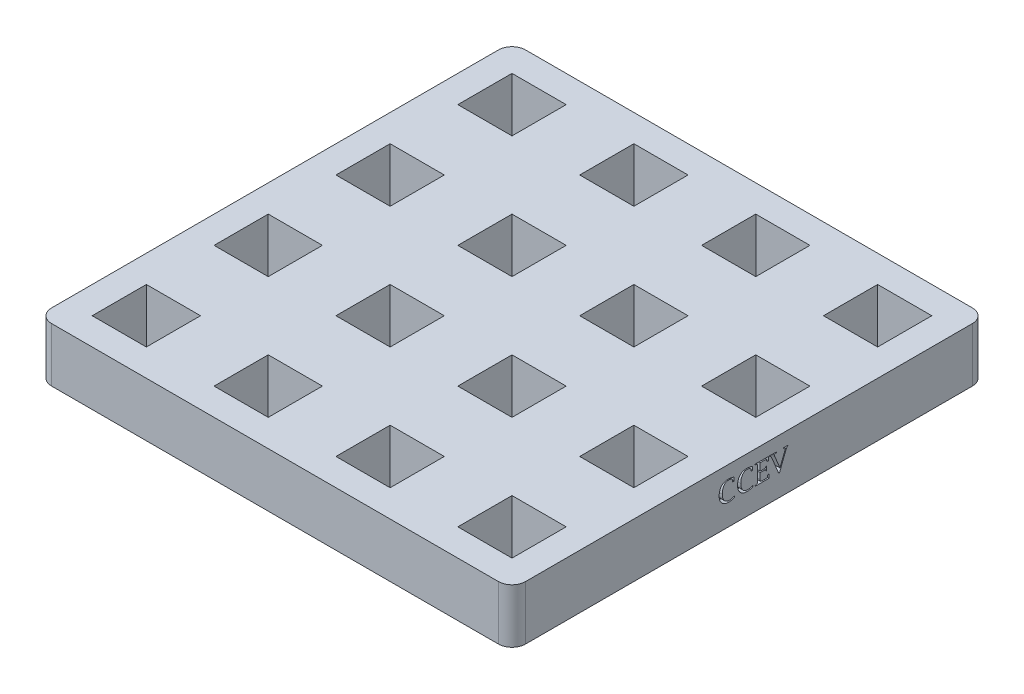
SolidWorks part; units mm, degrees
ref_plane "Front Plane" through (0, 0, 0) normal (0, 0, 1) x (1, 0, 0)
ref_plane "Top Plane" through (0, 0, 0) normal (0, 1, 0) x (1, 0, 0)
ref_plane "Right Plane" through (0, 0, 0) normal (1, 0, 0) x (0, 0, -1)
sketch "Sketch1" plane through (0, 0, 0) normal (0, 1, 0) x (1, 0, 0)
  line L0 (27.94, -5.08) -> (27.94, -15.24)
  line L1 (0, 0) -> (88.9, 0)
  line L2 (0, 0) -> (0, -88.9)
  line L3 (0, -88.9) -> (88.9, -88.9)
  line L4 (88.9, 0) -> (88.9, -88.9)
  line L5 (5.08, -5.08) -> (15.24, -5.08)
  line L6 (5.08, -5.08) -> (5.08, -15.24)
  line L7 (5.08, -15.24) -> (15.24, -15.24)
  line L8 (15.24, -5.08) -> (15.24, -15.24)
  line L9 (27.94, -5.08) -> (38.1, -5.08)
  line L10 (38.1, -5.08) -> (38.1, -15.24)
  line L11 (27.94, -15.24) -> (38.1, -15.24)
  line L12 (50.8, -5.08) -> (50.8, -15.24)
  line L13 (50.8, -5.08) -> (60.96, -5.08)
  line L14 (60.96, -5.08) -> (60.96, -15.24)
  line L15 (50.8, -15.24) -> (60.96, -15.24)
  line L16 (73.66, -5.08) -> (73.66, -15.24)
  line L17 (73.66, -5.08) -> (83.82, -5.08)
  line L18 (83.82, -5.08) -> (83.82, -15.24)
  line L19 (73.66, -15.24) -> (83.82, -15.24)
  line L20 (27.94, -27.94) -> (27.94, -38.1)
  line L21 (27.94, -27.94) -> (38.1, -27.94)
  line L22 (38.1, -27.94) -> (38.1, -38.1)
  line L23 (27.94, -38.1) -> (38.1, -38.1)
  line L24 (50.8, -27.94) -> (50.8, -38.1)
  line L25 (50.8, -27.94) -> (60.96, -27.94)
  line L26 (60.96, -27.94) -> (60.96, -38.1)
  line L27 (50.8, -38.1) -> (60.96, -38.1)
  line L28 (73.66, -27.94) -> (73.66, -38.1)
  line L29 (73.66, -27.94) -> (83.82, -27.94)
  line L30 (83.82, -27.94) -> (83.82, -38.1)
  line L31 (73.66, -38.1) -> (83.82, -38.1)
  line L32 (27.94, -50.8) -> (27.94, -60.96)
  line L33 (27.94, -50.8) -> (38.1, -50.8)
  line L34 (38.1, -50.8) -> (38.1, -60.96)
  line L35 (27.94, -60.96) -> (38.1, -60.96)
  line L36 (50.8, -50.8) -> (50.8, -60.96)
  line L37 (50.8, -50.8) -> (60.96, -50.8)
  line L38 (60.96, -50.8) -> (60.96, -60.96)
  line L39 (50.8, -60.96) -> (60.96, -60.96)
  line L40 (73.66, -50.8) -> (73.66, -60.96)
  line L41 (73.66, -50.8) -> (83.82, -50.8)
  line L42 (83.82, -50.8) -> (83.82, -60.96)
  line L43 (73.66, -60.96) -> (83.82, -60.96)
  line L44 (27.94, -73.66) -> (27.94, -83.82)
  line L45 (27.94, -73.66) -> (38.1, -73.66)
  line L46 (38.1, -73.66) -> (38.1, -83.82)
  line L47 (27.94, -83.82) -> (38.1, -83.82)
  line L48 (50.8, -73.66) -> (50.8, -83.82)
  line L49 (50.8, -73.66) -> (60.96, -73.66)
  line L50 (60.96, -73.66) -> (60.96, -83.82)
  line L51 (50.8, -83.82) -> (60.96, -83.82)
  line L52 (73.66, -73.66) -> (73.66, -83.82)
  line L53 (73.66, -73.66) -> (83.82, -73.66)
  line L54 (83.82, -73.66) -> (83.82, -83.82)
  line L55 (73.66, -83.82) -> (83.82, -83.82)
  line L56 (5.08, -27.94) -> (5.08, -38.1)
  line L57 (5.08, -27.94) -> (15.24, -27.94)
  line L58 (15.24, -27.94) -> (15.24, -38.1)
  line L59 (5.08, -38.1) -> (15.24, -38.1)
  line L60 (5.08, -50.8) -> (5.08, -60.96)
  line L61 (5.08, -50.8) -> (15.24, -50.8)
  line L62 (15.24, -50.8) -> (15.24, -60.96)
  line L63 (5.08, -60.96) -> (15.24, -60.96)
  line L64 (5.08, -73.66) -> (5.08, -83.82)
  line L65 (5.08, -73.66) -> (15.24, -73.66)
  line L66 (15.24, -73.66) -> (15.24, -83.82)
  line L67 (5.08, -83.82) -> (15.24, -83.82)
  line L68 (5.08, -5.08) -> (27.94, -5.08) construction
  point P9 (0, -44.45)
  dimension "D1" = 88.9
  dimension "D2" = 88.9
  dimension "D3" = 10.16
  dimension "D4" = 10.16
  dimension "D5" = 5.08
  dimension "D6" = 5.08
  dimension "D9" = 22.86
  dimension "D7" = 4
  dimension "D8" = 4
extrude "Boss-Extrude1" add sketch "Sketch1" along normal blind 10.16
sketch "Sketch3" plane through (88.9, 0, 0) normal (1, 0, 0) x (0, 0, -1)
  text T0 "CCEV" font "Lucida Bright" height in points 14
extrude "Cut-Extrude2" cut sketch "Sketch3" against normal blind 1.27
fillet "Fillet1" radius 2.54 4 edges at (0, 5.08, 88.9) (0, 5.08, 0) (88.9, 5.08, 88.9) (88.9, 5.08, 0)
